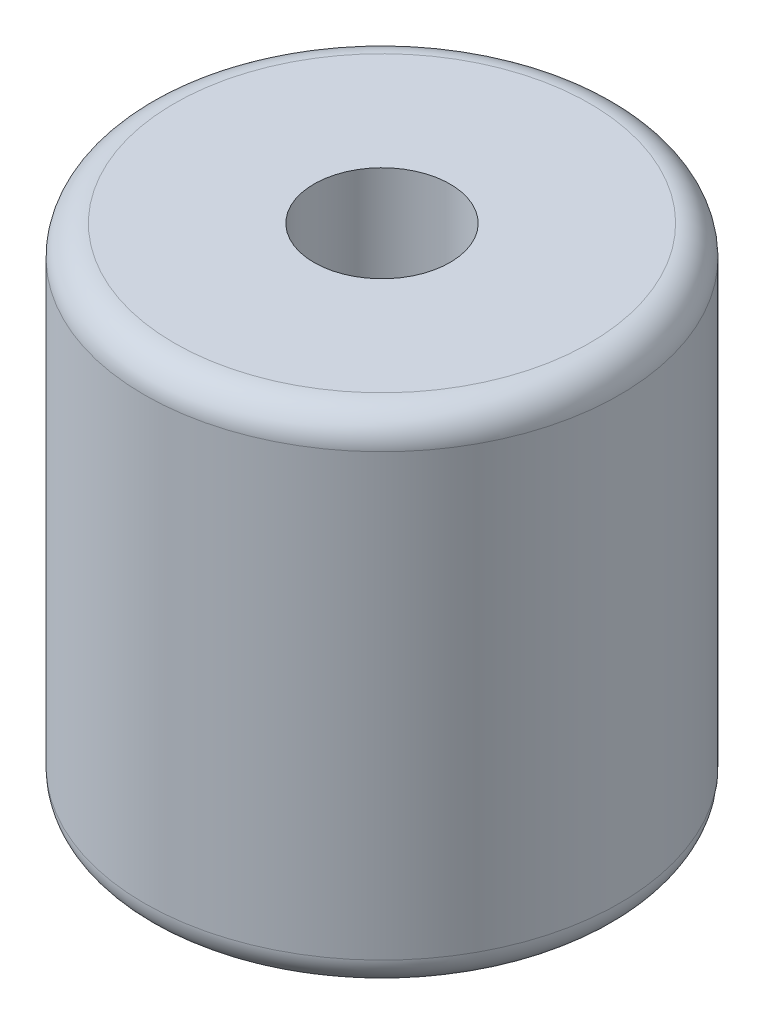
SolidWorks part; units mm, degrees
ref_plane "Front Plane" through (0, 0, 0) normal (0, 0, 1) x (1, 0, 0)
ref_plane "Top Plane" through (0, 0, 0) normal (0, 1, 0) x (1, 0, 0)
ref_plane "Right Plane" through (0, 0, 0) normal (1, 0, 0) x (0, 0, -1)
sketch "Sketch1" plane through (0, 0, 0) normal (0, 1, 0) x (1, 0, 0)
  circle A0 centre (0, 0) radius 6.0325
  dimension "D1" = 12.065
extrude "Boss-Extrude1" add sketch "Sketch1" along normal blind 12.7
fillet "Fillet1" radius 0.76 2 edges at (0, 0, 6.0325) (0, 12.7, 6.0325)
hole_wizard "#8-32 Tapped Hole1" positions "Sketch2" profile "Sketch4" tap size "#8-32" standard "ANSI Inch"
sketch "Sketch2" plane through (0, 12.7, 0) normal (0, 1, 0) x (1, 0, 0)
  point P0 (0, 0)
cosmetic thread "Hole Thread1" parameters "D1"=11.43, "D2"=4.1656
sketch "Sketch4" plane through (0, 12.7, 0) normal (1, 0, 0) x (0, 0, 1)
  line L0 (0, 0) -> (0, 12.4678)
  line L1 (0, 12.4678) -> (1.7272, 11.43)
  line L2 (1.7272, 11.43) -> (1.7272, 0)
  line L5 (1.7272, 0) -> (0, 0)
  line L10 (0, 12.4678) -> (-1.7272, 11.43) construction
  line L11 (0, -6.35) -> (0, 107.95) construction
  dimension "Tap Drill Dia." = 3.4544
  dimension "Tap Drill Depth" = 11.43
  dimension "Drill Angle" = 118
